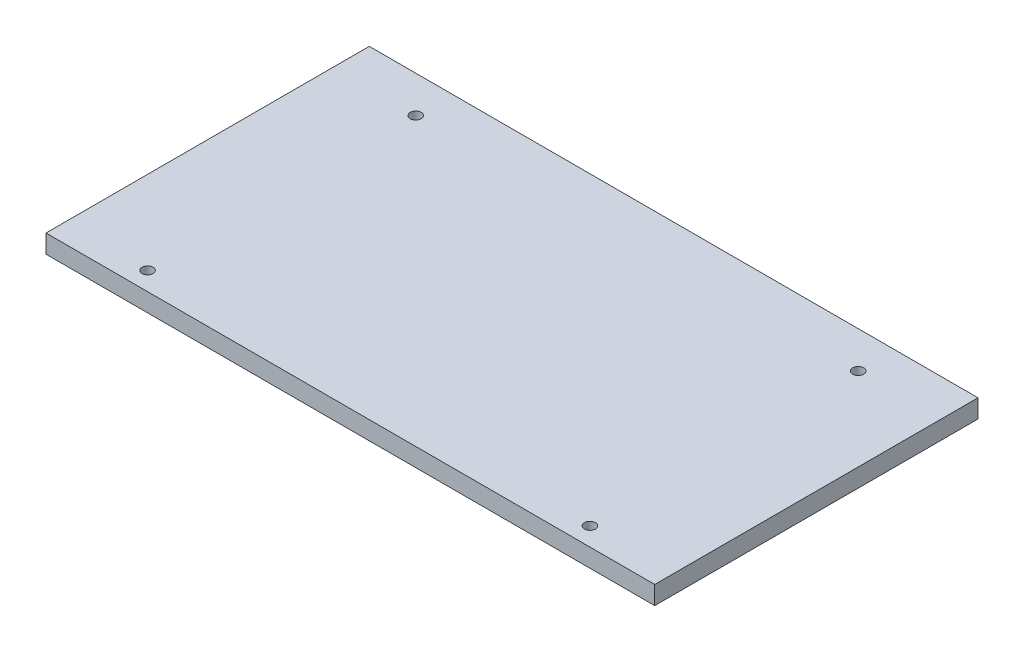
SolidWorks part; units mm, degrees
ref_plane "Front Plane" through (0, 0, 0) normal (0, 0, 1) x (1, 0, 0)
ref_plane "Top Plane" through (0, 0, 0) normal (0, 1, 0) x (1, 0, 0)
ref_plane "Right Plane" through (0, 0, 0) normal (1, 0, 0) x (0, 0, -1)
sketch "Sketch1" plane through (0, 0, 0) normal (0, 1, 0) x (1, 0, 0)
  line L0 (-60.5421, -44) -> (-57.5421, -44)
  line L1 (79.0231, -44) -> (79.0231, -34)
  line L2 (79.0231, -34) -> (-76.6797, -34)
  line L3 (-76.6797, -34) -> (-76.6797, -44)
  line L4 (-76.6797, 24) -> (79.0231, 24)
  line L5 (79.0231, 24) -> (79.0231, 44)
  line L6 (62.8855, 44) -> (59.8855, 44)
  line L7 (-76.6797, 44) -> (-76.6797, 24)
  line L8 (-76.6797, 44) -> (-76.6797, -44)
  line L9 (-60.5421, 44) -> (-57.5421, 44)
  line L10 (-60.5421, -44) -> (-57.5421, -44)
  line L11 (79.0231, 44) -> (79.0231, -44)
  line L12 (-76.6797, 34) -> (79.0231, 34) construction
  line L13 (62.8855, 44) -> (59.8855, 44)
  line L14 (59.8855, -44) -> (62.8855, -44)
  line L15 (-60.5421, -44) -> (-57.5421, -44)
  line L16 (-57.5421, 44) -> (-60.5421, 44)
  line L17 (-76.6797, -39) -> (79.0231, -39) construction
  line L18 (-57.5421, 44) -> (-60.5421, 44)
  line L19 (59.8855, 44) -> (62.8855, 44)
  line L20 (59.8855, -44) -> (62.8855, -44)
  line L21 (59.8855, -44) -> (62.8855, -44)
  line L22 (-59.0421, 44) -> (-59.0421, 24) construction
  line L23 (61.3855, 44) -> (61.3855, 24) construction
  line L24 (61.3855, -44) -> (61.3855, -34) construction
  line L25 (-59.0421, -44) -> (-59.0421, -34) construction
  line L26 (-76.6797, 24) -> (79.0231, 24)
  line L27 (79.0231, 24) -> (79.0231, 44)
  line L28 (79.0231, 44) -> (-76.6797, 44)
  line L29 (-76.6797, 44) -> (-76.6797, 24)
  line L30 (-76.6797, -44) -> (79.0231, -44)
  circle A0 centre (-59.0421, -39) radius 1.5
  circle A1 centre (61.3855, -39) radius 1.5
  circle A2 centre (61.3855, 34) radius 1.5
  circle A3 centre (-59.0421, 34) radius 1.5
  dimension "D1" = 3
extrude "Boss-Extrude2" add sketch "Sketch1" along normal blind 5 contours L11 L4 L8 L2 | L5 L28 L6 L9 L7 L4 A3 A2 | L3 L30 L0 L14 L1 L2 A1 A0
sketch "Sketch2" plane through (0, 5, 0) normal (0, 1, 0) x (1, 0, 0)
  line L0 (79.0231, 44) -> (79.0231, -44)
  line L1 (79.0231, 44) -> (84.0231, 44)
  line L2 (79.0231, -44) -> (84.0231, -44)
  line L3 (84.0231, 44) -> (84.0231, -44)
  line L4 (-76.6797, 44) -> (-76.6797, -44)
  line L5 (-76.6797, 44) -> (-81.6797, 44)
  line L6 (-76.6797, -44) -> (-81.6797, -44)
  line L7 (-81.6797, 44) -> (-81.6797, -44)
  dimension "D1" = 5
  dimension "D2" = 5
extrude "Boss-Extrude3" add sketch "Sketch2" against normal up to surface (5 mm away) up to face at (1.1717, 0, 0)
